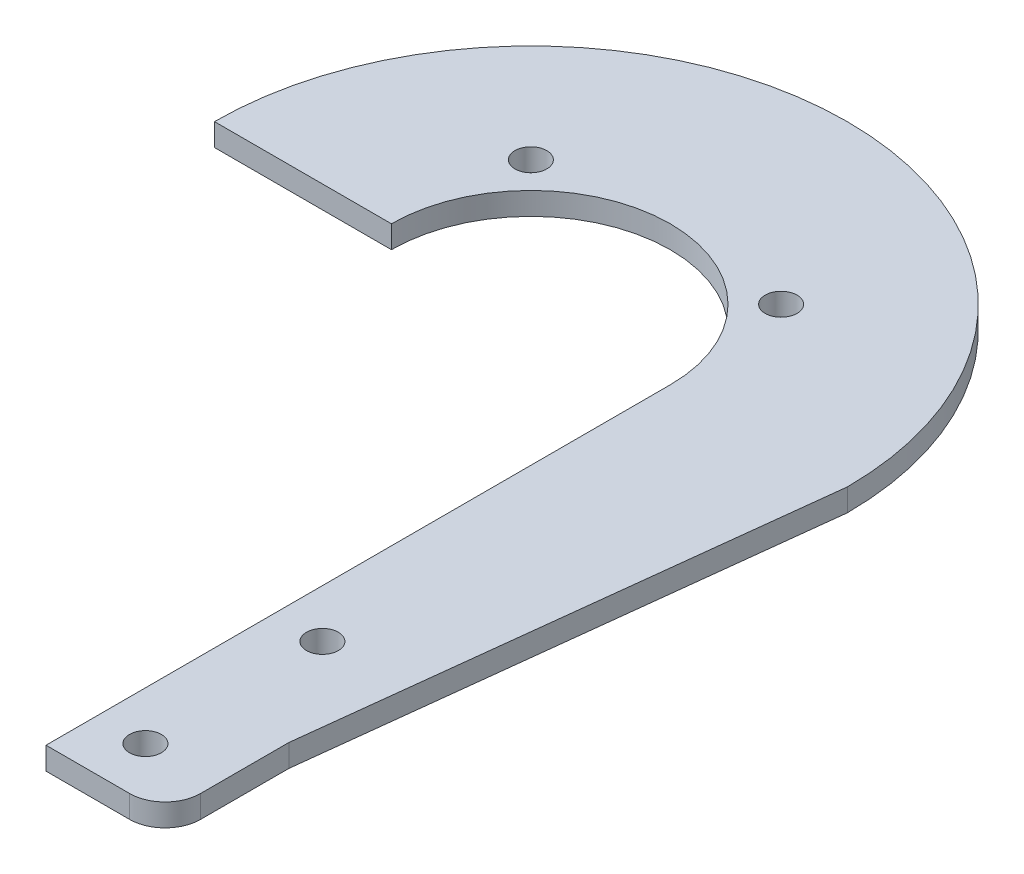
SolidWorks part; units mm, degrees
other "Markup1"
sketch "Sketch3" plane through (-44.7, 3.175, -44.7) normal (0, 1, 0) x (1, 0, 0)
ref_plane "Front Plane" through (0, 0, 0) normal (0, 0, 1) x (1, 0, 0)
ref_plane "Top Plane" through (0, 0, 0) normal (0, 1, 0) x (1, 0, 0)
ref_plane "Right Plane" through (0, 0, 0) normal (1, 0, 0) x (0, 0, -1)
sketch "Sketch2" plane through (0, 0, 0) normal (0, 1, 0) x (1, 0, 0)
  line L0 (19.7, -88.2) -> (31.525, -88.2)
  line L1 (36.525, -83.2) -> (36.525, -70.7)
  line L2 (19.7, -88.2) -> (19.7, 0)
  line L3 (36.525, -70.7) -> (44.7, 0)
  line L4 (-44.7, 0) -> (-19.7, 0)
  line L5 (26.525, -80.975) -> (26.525, -55.975) construction
  line L6 (0, 0) -> (17.6777, 17.6777) construction
  line L7 (0, 0) -> (-17.6777, 17.6777) construction
  arc A0 (44.7, 0) -> (-44.7, 0) centre (0, 0) ccw
  arc A1 (19.7, 0) -> (-19.7, 0) centre (0, 0) ccw
  circle A2 centre (26.525, -80.975) radius 2.25
  circle A3 centre (26.525, -55.975) radius 2.25
  arc A4 (31.525, -88.2) -> (36.525, -83.2) centre (31.525, -83.2) ccw
  circle A5 centre (-17.6777, 17.6777) radius 2.25
  circle A6 centre (17.6777, 17.6777) radius 2.25
  point P20 (36.525, -88.2)
  dimension "D4" = 4.5
  dimension "D5" = 5
  dimension "D8" = 19.7
  dimension "D9" = 4.5
  dimension "D1" = 16.825
  dimension "D2" = 25
  dimension "D3" = 25
  dimension "D6" = 7.225
  dimension "D7" = 10
  dimension "D10" = 45
  dimension "D11" = 90
  dimension "D12" = 25
  dimension "D13" = 88.2
  dimension "D14" = 17.5
extrude "Boss-Extrude1" add sketch "Sketch2" along normal blind 3.175
